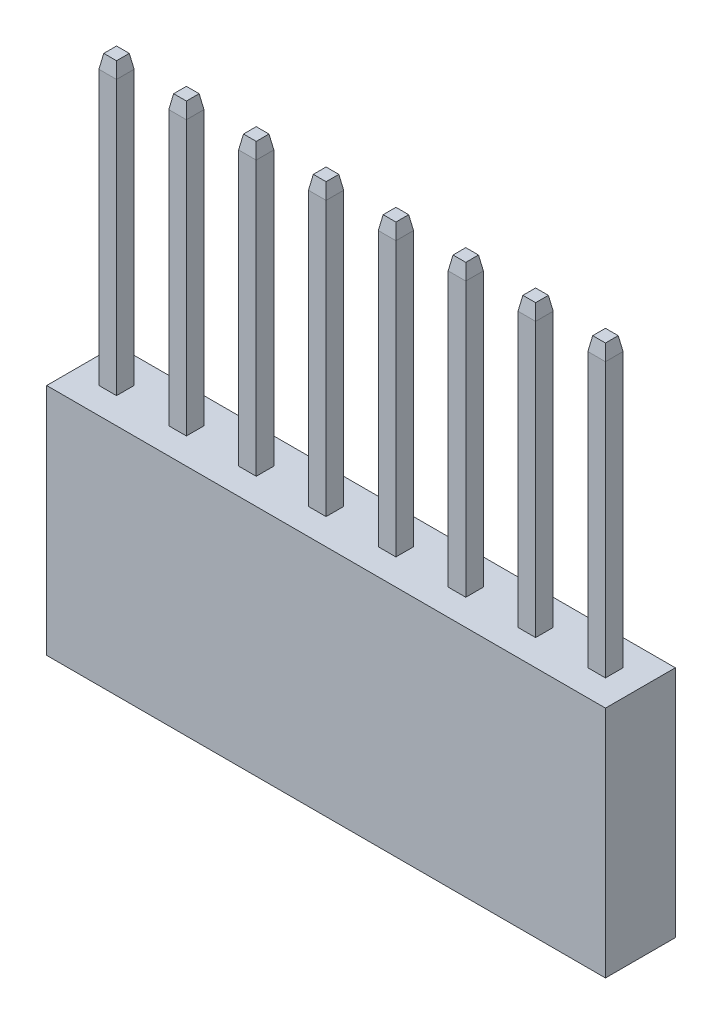
SolidWorks part; units mm, degrees
ref_plane "Front Plane" through (0, 0, 0) normal (0, 0, 1) x (1, 0, 0)
ref_plane "Top Plane" through (0, 0, 0) normal (0, 1, 0) x (1, 0, 0)
ref_plane "Right Plane" through (0, 0, 0) normal (1, 0, 0) x (0, 0, -1)
sketch "Sketch1" plane through (0, 0, 0) normal (0, 1, 0) x (1, 0, 0)
  line L1 (1.27, 1.27) -> (-1.27, 1.27)
  line L2 (1.27, 1.27) -> (1.27, -1.27)
  line L3 (1.27, -1.27) -> (-1.27, -1.27)
  line L4 (-1.27, 1.27) -> (-1.27, -1.27)
  line L5 (1.27, 1.27) -> (-1.27, -1.27) construction
  line L6 (1.27, -1.27) -> (-1.27, 1.27) construction
  point P0 (0, 0)
  dimension "D1" = 2.54
extrude "Boss-Extrude1" add sketch "Sketch1" along normal blind 8.5
sketch "Sketch2" plane through (0, 0, 0) normal (0, 1, 0) x (1, 0, 0)
  line L1 (0.32, 0.32) -> (-0.32, 0.32)
  line L2 (0.32, 0.32) -> (0.32, -0.32)
  line L3 (0.32, -0.32) -> (-0.32, -0.32)
  line L4 (-0.32, 0.32) -> (-0.32, -0.32)
  line L5 (0.32, 0.32) -> (-0.32, -0.32) construction
  line L6 (0.32, -0.32) -> (-0.32, 0.32) construction
  point P0 (0, 0)
  dimension "D1" = 0.64
extrude "Boss-Extrude2" add sketch "Sketch2" along normal blind 18.9595
chamfer "Chamfer1" distance 0.5 angle 10 4 edges at (0, 18.9595, -0.32) (0.32, 18.9595, 0) (0, 18.9595, 0.32) (-0.32, 18.9595, 0)
sketch "Sketch3" plane through (0, 0, 0) normal (0, -1, 0) x (1, 0, 0)
  line L1 (0.32, 0.32) -> (-0.32, 0.32)
  line L2 (0.32, 0.32) -> (0.32, -0.32)
  line L3 (0.32, -0.32) -> (-0.32, -0.32)
  line L4 (-0.32, 0.32) -> (-0.32, -0.32)
  line L5 (0.32, 0.32) -> (-0.32, -0.32) construction
  line L6 (0.32, -0.32) -> (-0.32, 0.32) construction
  point P0 (0, 0)
  dimension "D1" = 0.64
extrude "Cut-Extrude1" cut sketch "Sketch3" against normal blind 6
chamfer "Chamfer2" distance 0.64 angle 45 4 edges at (0, 0, -0.32) (-0.32, 0, 0) (0, 0, 0.32) (0.32, 0, 0)
pattern_linear "LPattern1" count 8 spacing 2.54 along (-1, 0, 0) of "Boss-Extrude1", "Boss-Extrude2", "Chamfer1", "Cut-Extrude1", "Chamfer2"
equation "\"NumHeaders\"=2"
